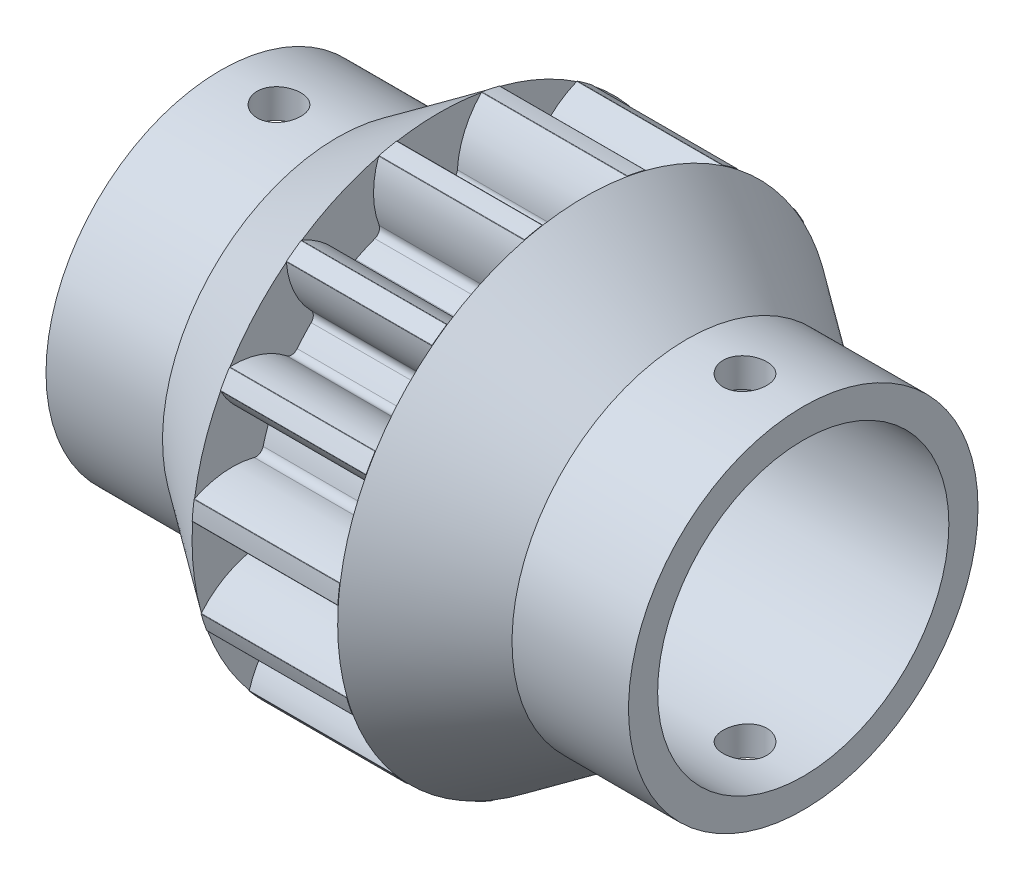
SolidWorks part; units mm, degrees
ref_plane "Plane1" through (0, 0, 0) normal (0, 0, 1) x (1, 0, 0)
ref_plane "Plane2" through (0, 0, 0) normal (0, 1, 0) x (1, 0, 0)
ref_plane "Plane3" through (0, 0, 0) normal (1, 0, 0) x (0, 0, -1)
sketch "HoldingSke" plane through (0, 0, 0) normal (0, 1, 0) x (1, 0, 0)
  line L0 (0, 0) -> (0.9659, -0.2588)
  line L1 (-15, 0) -> (100, 0) construction
  line L2 (0, 0) -> (-2.1039, 2.3779)
  line L3 (0, 0) -> (-11.863, 4.5341)
  line L4 (0, 0) -> (8.3417, 2.2352)
  line L5 (0, 0) -> (-18.7391, -6.9891)
  line L6 (0, 0) -> (-4.1448, -2.7965)
  line L7 (-2.1039, 2.3779) -> (2.2011, 21.9091)
  line L8 (-76.2, 54.61) -> (-74.4, 54.61)
  line L9 (-67.7845, 28.3722) -> (-49.3413, 33.142)
  line L10 (-76.2, 71.12) -> (104.1128, 71.12)
  line L11 (0, 0) -> (-5, 0)
  line L12 (-76.2, 101.6) -> (-76.162, 101.6)
  line L13 (24.9733, 27.94) -> (52.9518, 28.4284)
  line L14 (24.9733, 27.94) -> (24.9743, 27.94)
  line L15 (24.9733, 27.94) -> (100.4006, 29.5858)
  line L16 (-63.627, -1) -> (-12.827, -1)
  circle A0 centre (0, 0) radius 5
  circle A1 centre (0, 0) radius 6
  circle A2 centre (0, 0) radius 6
  circle A3 centre (0, 0) radius 5
  dimension "MHD" = 12
  dimension "Hub_dia" = 12
  dimension "Bore" = 10
  dimension "MBD" = 10
  dimension "Num_teeth" = 15
  dimension "Pitch_radius" = 180.3128
  dimension "Pitch" = 1
  dimension "Width" = 5
  dimension "Overall_len" = 20
  dimension "Show_teeth" = 15
  dimension "Thickness" = 5
  dimension "OAL" = 20.0001
  dimension "T_dim" = 1.8
  dimension "Ap" = 14.5
  dimension "H" = 19.05
  dimension "Backlash" = 0.038
  dimension "Addendum_fac" = 1
  dimension "Dedendum_fac" = 1.25
  dimension "Clearance_fac" = 0.25
  dimension "Dedendum_add" = 0.001
  dimension "Module" = 1
sketch "BasProSke" plane through (0, 0, 0) normal (0, 1, 0) x (1, 0, 0)
  line L0 (-10, 0) -> (60, 0) construction
  line L1 (0, 0) -> (0, 8.5)
  line L2 (0, 0) -> (5, 0)
  line L3 (5, 0) -> (5, 8.5)
  line L4 (5, 8.5) -> (0, 8.5)
  dimension "Diameter" = 17
  dimension "Thickness" = 5
revolve "Base-Revolve" add sketch "BasProSke" angle 360 about L0
sketch "TooCutSke" plane through (0, 0, 0) normal (1, 0, 0) x (0, 0, -1)
  line L1 (0, 0) -> (0, 107) construction
  line L2 (0, 0) -> (-0.8504, 7.4516) construction
  line L3 (0, 0) -> (-3.1044, 14.6049) construction
  line L4 (-0.8504, 7.4516) -> (-1.5522, 7.3025) construction
  arc A0 (0.6195, 6.2182) -> (-0.6195, 6.2182) centre (0, 0) ccw
  arc A1 (1.4773, 8.3964) -> (-1.4773, 8.3964) centre (0, 0) ccw
  circle A2 centre (0, 0) radius 7.5 construction
  circle A3 centre (0, 0) radius 7.2611 construction
  arc A4 (-0.6195, 6.2182) -> (-1.4773, 8.3964) centre (-3.6186, 6.2952) ccw
  arc A5 (1.4773, 8.3964) -> (0.6195, 6.2182) centre (3.6186, 6.2952) ccw
  dimension "Root_dia" = 12.498
  dimension "Overcut_dia" = 17.0508
  dimension "Pitch_dia" = 15
  dimension "Base_dia" = 14.5222
  dimension "Flank_rad" = 3
  dimension "Half_ang" = 12
  dimension "Half_CT" = 0.7175
extrude "ToothCut" cut sketch "TooCutSke" along normal through all
fillet "Breaks" radius 0.02 2 edges at (2.5, 8.3744, -1.4559) (2.5, 8.3744, 1.4559)
fillet "RootFillets" radius 0.251 2 edges at (2.5, 6.2182, -0.6195) (2.5, 6.2182, 0.6195)
pattern_circular "TeethCuts" count 15 every 24 about axis through (-10, 0, 0) along (1, 0, 0) of "ToothCut", "RootFillets", "Breaks"
sketch "HubNeaOneSke" plane through (0, 0, 0) normal (-1, 0, 0) x (0, 0, 1)
  circle A0 centre (0, 0) radius 6
  dimension "Diameter" = 12
extrude "HubNearOne" [suppressed] add sketch "HubNeaOneSke" along normal blind 15.0001
sketch "HubNeaBotSke" plane through (0, 0, 0) normal (-1, 0, 0) x (0, 0, 1)
  circle A0 centre (0, 0) radius 6
  dimension "Diameter" = 12
extrude "HubNearBoth" add sketch "HubNeaBotSke" along normal blind 7.5
ref_plane "FarPln" through (5, 0, 0) normal (1, 0, 0) x (0, 0, -1)
sketch "HubFarSke" plane through (5, 0, 0) normal (1, 0, 0) x (0, 0, -1)
  circle A0 centre (0, 0) radius 6
  dimension "Diameter" = 12
extrude "HubFar" add sketch "HubFarSke" along normal blind 7.5
sketch "BorSke" plane through (0, 0, 0) normal (1, 0, 0) x (0, 0, -1)
  circle A0 centre (0, 0) radius 5
  dimension "Diameter" = 10
extrude "Bore" cut sketch "BorSke" along normal mid plane 40.0001
sketch "KeySke" plane through (0, 0, 0) normal (1, 0, 0) x (0, 0, -1)
  line L0 (-2, 0) -> (-2, 6.8)
  line L1 (-2, 6.8) -> (2, 6.8)
  line L2 (2, 6.8) -> (2, 0)
  line L3 (0, 0) -> (0, 34) construction
  line L4 (-2, 0) -> (2, 0)
  dimension "Offset" = 6.8
  dimension "Width" = 4
extrude "Keyway" [suppressed] cut sketch "KeySke" along normal mid plane 40.0001
pattern_circular "Keyway2" [suppressed] count 2 every 90 about axis through (-10, 0, 0) along (1, 0, 0)
sketch "Schizzo5" plane through (0, 0, 0) normal (0, 0, 1) x (1, 0, 0)
  line L0 (12.5, 0) -> (-7.5, 0) construction
  line L1 (12.5, -6) -> (12.5, 6) construction
  line L2 (-7.5, 5) -> (-7.5, -5) construction
sketch "Schizzo8" plane through (0, 0, 0) normal (0, 1, 0) x (1, 0, 0)
  line L0 (12.5, 0) -> (-7.5, 0) construction
  line L1 (-7.5, 6) -> (-7.5, -6) construction
  line L2 (12.5, -6) -> (12.5, 6) construction
  circle A0 centre (-5.5, 0) radius 0.75
  circle A1 centre (10.5, 0) radius 0.75
  dimension "D3" = 1.5
  dimension "D4" = 1.5
  dimension "D1" = 2
  dimension "D2" = 2
extrude "Taglio-Estrusione2" cut sketch "Schizzo8" against normal through all both and the other way through all
sketch "Schizzo9" plane through (0, 0, 0) normal (0, 0, 1) x (1, 0, 0)
  line L0 (12.5, -6) -> (8.5, -6)
  line L1 (5, -6) -> (9.75, -6) construction
  line L2 (8.5, -6) -> (5, -8.485)
  line L3 (5, -8.485) -> (5, -6)
  line L4 (5, -7.6202) -> (5, -5.6045) construction
  line L5 (5, -6) -> (9.75, -6) construction
  line L6 (5, -6) -> (8.5, -6)
  line L7 (-7.5, -6) -> (-3.5, -6)
  line L8 (-4.75, -6) -> (0, -6) construction
  line L9 (-3.5, -6) -> (0, -8.485)
  line L10 (0, -8.485) -> (0, -6)
  line L11 (-4.75, -6) -> (0, -6) construction
  line L12 (0, -6) -> (-3.5, -6)
  dimension "D1" = 4
  dimension "D2" = 4
revolve "Rivoluzione1" add sketch "Schizzo9" angle 360 about L0
equation "' \"Module@HoldingSke\" = 6.35"
equation "' \"Num_teeth@HoldingSke\" = 12"
equation "' \"Ap@HoldingSke\" =  20"
equation "' \"Width@HoldingSke\" = 0.5 * 25.4"
equation "' \"Hub_dia@HoldingSke\"= 1 * 25.4"
equation "' \"Overall_len@HoldingSke\" = 1.0 * 25.4"
equation "' \"Bore@HoldingSke\" = 0.75 * 25.4"
equation "' \"T_dim@HoldingSke\" = 0.1 * 25.4"
equation "' \"Width@KeySke\" = 0.25 * 25.4"
equation "' \"Show_teeth@HoldingSke\" = 13"
equation "' \"Backlash@HoldingSke\" = 0.009 * 25.4"
equation "' \"Addendum_fac@HoldingSke\" = 1.0"
equation "' \"Dedendum_fac@HoldingSke\" = 1.25"
equation "' \"Dedendum_add@HoldingSke\" = 0.00005 * 25.4"
equation "' \"Clearance_fac@HoldingSke\" = 0.25"
equation "\"Pitch@HoldingSke\" = 1 / \"Module@HoldingSke\""
equation "\"Overcut_dia@TooCutSke\" = (\"Num_teeth@HoldingSke\" + 2 * \"Addendum_fac@HoldingSke\") / \"Pitch@HoldingSke\" + 0.002 * 25.4"
equation "\"Pitch_dia@TooCutSke\" = \"Num_teeth@HoldingSke\" / \"Pitch@HoldingSke\""
equation "\"Base_dia@TooCutSke\" = \"Num_teeth@HoldingSke\" / \"Pitch@HoldingSke\" * cos((\"Ap@HoldingSke\"  * 3.14159265 / 180))"
equation "\"Root_dia@TooCutSke\" = (\"Num_teeth@HoldingSke\" + 2) / \"Pitch@HoldingSke\" - 2 * (\"Addendum_fac@HoldingSke\" + \"Dedendum_fac@HoldingSke\") / \"Pitch@HoldingSke\" - \"Dedendum_add@HoldingSke\" * 2"
equation "\"Half_ang@TooCutSke\" = 180 / \"Num_teeth@HoldingSke\""
equation "\"Half_CT@TooCutSke\" = \"Num_teeth@HoldingSke\" / \"Pitch@HoldingSke\" * sin((3.14159265 / 2 / \"Num_teeth@HoldingSke\")) / 2 - 7 * \"Backlash@HoldingSke\" / 4"
equation "\"Flank_rad@TooCutSke\" = \"Num_teeth@HoldingSke\" / \"Pitch@HoldingSke\" / 5"
equation "\"Radius@RootFillets\" = \"Clearance_fac@HoldingSke\" / \"Pitch@HoldingSke\" + \"Dedendum_add@HoldingSke\""
equation "\"Break_rad@Breaks\" = 0.02 / \"Pitch@HoldingSke\""
equation "\"Thickness@HoldingSke\" = \"Width@HoldingSke\""
equation "\"OAL@HoldingSke\" = \"Thickness@HoldingSke\""
equation "\"MHD@HoldingSke\" = (\"Num_teeth@HoldingSke\" + 2) / \"Pitch@HoldingSke\" - 2 * (\"Addendum_fac@HoldingSke\" + \"Dedendum_fac@HoldingSke\")  / \"Pitch@HoldingSke\" - \"Dedendum_add@HoldingSke\" * 2"
equation "\"MBD@HoldingSke\" = (\"Num_teeth@HoldingSke\" + 2) / \"Pitch@HoldingSke\" - 2 * (\"Addendum_fac@HoldingSke\" + \"Dedendum_fac@HoldingSke\")  / \"Pitch@HoldingSke\" - \"Dedendum_add@HoldingSke\" * 2 - 0.002 * 25.4"
equation "\"MHD@HoldingSke\" = ((sgn( \"MHD@HoldingSke\" - \"Hub_dia@HoldingSke\" )-1)*( \"MHD@HoldingSke\" - \"Hub_dia@HoldingSke\" ))/-2+ \"Hub_dia@HoldingSke\""
equation "\"MBD@HoldingSke\" = ((sgn( \"MBD@HoldingSke\" - \"Bore@HoldingSke\" )-1)*( \"MBD@HoldingSke\" - \"Bore@HoldingSke\" ))/-2+ \"Bore@HoldingSke\""
equation "\"OAL@HoldingSke\" = ((sgn( \"OAL@HoldingSke\" - \"Overall_len@HoldingSke\" )+1)*( \"OAL@HoldingSke\" - \"Overall_len@HoldingSke\" ))/2 + \"Overall_len@HoldingSke\" + 0.000002 * 25.4"
equation "\"Num_teeth@TeethCuts\" = int( \"Show_teeth@HoldingSke\" ) + 1"
equation "\"Num_teeth@TeethCuts\" = ((sgn( \"Num_teeth@TeethCuts\" - \"Num_teeth@HoldingSke\" )-1)*( \"Num_teeth@TeethCuts\" - \"Num_teeth@HoldingSke\" ))/-2+ \"Num_teeth@HoldingSke\""
equation "\"Num_teeth@TeethCuts\" = ((sgn( \"Num_teeth@TeethCuts\" - 2.0)+1)*( \"Num_teeth@TeethCuts\" - 2.0))/2 +2.0"
equation "\"Angle@TeethCuts\" = 360.0 / \"Num_teeth@HoldingSke\""
equation "\"Diameter@BasProSke\" = (\"Num_teeth@HoldingSke\" + 2 * \"Addendum_fac@HoldingSke\") / \"Pitch@HoldingSke\""
equation "\"Thickness@BasProSke\"  = \"Thickness@HoldingSke\""
equation "' \"Fillet_rad@BasProSke\" =  \"Thickness@HoldingSke\" * 0.05"
equation "\"MHD@HoldingSke\" = ((sgn( \"MHD@HoldingSke\" - \"Root_dia@TooCutSke\" )-1)*( \"MHD@HoldingSke\" - \"Root_dia@TooCutSke\" ))/-2+ \"Root_dia@TooCutSke\""
equation "\"Diameter@HubNeaOneSke\" = \"MHD@HoldingSke\""
equation "\"Length@HubNearOne\" = \"OAL@HoldingSke\" - \"Thickness@BasProSke\""
equation "\"Diameter@HubNeaBotSke\" = \"MHD@HoldingSke\""
equation "\"Length@HubNearBoth\" = ( \"OAL@HoldingSke\" - \"Thickness@BasProSke\" ) / 2.0"
equation "\"Thickness@FarPln\" = \"Thickness@BasProSke\""
equation "\"Diameter@HubFarSke\" = \"MHD@HoldingSke\""
equation "\"Length@HubFar\" = ( \"OAL@HoldingSke\" - \"Thickness@BasProSke\" ) / 2.0"
equation "\"Diameter@BorSke\" = \"MBD@HoldingSke\""
equation "\"D1@Bore\" = \"OAL@HoldingSke\" * 2.0"
equation "\"D1@Keyway\" = \"OAL@HoldingSke\" * 2.0"
equation "\"Offset@KeySke\" = \"T_dim@HoldingSke\" + \"MBD@HoldingSke\" / 2.0"
